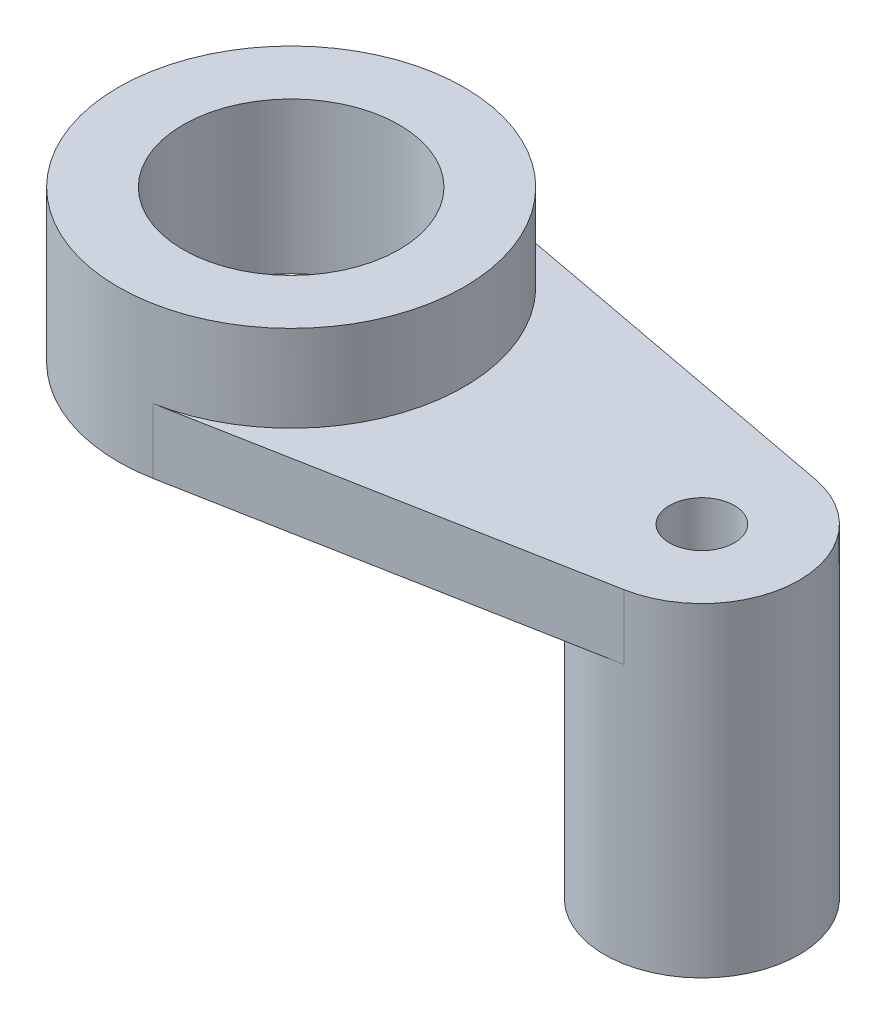
SolidWorks part; units mm, degrees
material "Galvanized Steel"
ref_plane "Front Plane" through (0, 0, 0) normal (0, 0, 1) x (1, 0, 0)
ref_plane "Top Plane" through (0, 0, 0) normal (0, 1, 0) x (1, 0, 0)
ref_plane "Right Plane" through (0, 0, 0) normal (1, 0, 0) x (0, 0, -1)
sketch "Sketch1" plane through (0, 0, 0) normal (0, 1, 0) x (1, 0, 0)
  line L0 (2.9474, 15.7262) -> (39.6579, 8.846)
  line L1 (2.9474, -15.7262) -> (39.6579, -8.846)
  circle A0 centre (0, 0) radius 10
  arc A1 (2.9474, 15.7262) -> (2.9474, -15.7262) centre (0, 0) ccw
  circle A2 centre (38, 0) radius 3
  arc A3 (39.6579, -8.846) -> (39.6579, 8.846) centre (38, 0) ccw
  point P3 (0, 0)
  dimension "D2" = 6
  dimension "D3" = 20
  dimension "D4" = 6
  dimension "D5" = 6
  dimension "D1" = 38
extrude "Boss-Extrude1" add sketch "Sketch1" along normal blind 6
sketch "Sketch2" plane through (0, 6, 0) normal (0, 1, 0) x (1, 0, 0)
  circle A0 centre (0, 0) radius 10
  circle A1 centre (0, 0) radius 16
extrude "Boss-Extrude2" add sketch "Sketch2" along normal blind 8
sketch "Sketch3" plane through (0, 0, 0) normal (0, -1, 0) x (1, 0, 0)
  circle A0 centre (38, 0) radius 3
  circle A1 centre (38, 0) radius 9
extrude "Boss-Extrude3" add sketch "Sketch3" along normal blind 24
